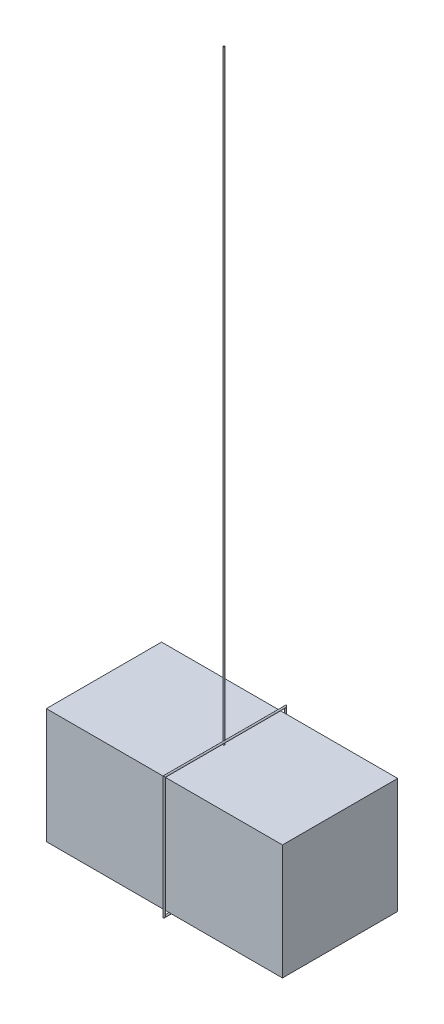
SolidWorks part; units mm, degrees
ref_plane "Front Plane" through (0, 0, 0) normal (0, 0, 1) x (1, 0, 0)
ref_plane "Top Plane" through (0, 0, 0) normal (0, 1, 0) x (1, 0, 0)
ref_plane "Right Plane" through (0, 0, 0) normal (1, 0, 0) x (0, 0, -1)
sketch "Sketch1" plane through (0, 0, 0) normal (0, 0, 1) x (1, 0, 0)
  line L0 (0, 0) -> (198.4375, 0)
  line L1 (198.4375, 0) -> (198.4375, -96.8375)
  line L2 (198.4375, -96.8375) -> (0, -96.8375)
  line L3 (0, -96.8375) -> (0, 0)
  dimension "D1" = 198.4375
  dimension "D2" = 96.8375
extrude "Extrude1" add sketch "Sketch1" along normal mid plane 96.8375
ref_plane "Plano1" through (101.6, 0, 0) normal (1, 0, 0) x (0, 0, -1)
sketch "Esboço1" plane through (101.6, 0, 0) normal (1, 0, 0) x (0, 0, -1)
  line L0 (48.4187, -96.8375) -> (48.4187, 0) construction
  line L1 (-50.9587, 2.54) -> (50.9587, 2.54)
  line L2 (-50.9587, 2.54) -> (-50.9588, -99.3775)
  line L3 (-50.9588, -99.3775) -> (50.9587, -99.3775)
  line L4 (50.9587, 2.54) -> (50.9587, -99.3775)
  line L5 (-50.9587, 2.54) -> (50.9587, -99.3775) construction
  line L6 (-50.9588, -99.3775) -> (50.9587, 2.54) construction
  line L7 (-48.4187, 0) -> (48.4187, 0) construction
  line L9 (-48.4187, -96.8375) -> (48.4187, -96.8375) construction
  point P0 (0, -48.4187)
  dimension "D1" = 2.54
  dimension "D2" = 2.54
  dimension "D3" = 2.54
sketch "Esboço2" plane through (0, 0, 0) normal (0, 0, 1) x (1, 0, 0)
  line L0 (101.6, 2.54) -> (101.6, -99.3775) construction
  line L1 (101.6, 2.54) -> (101.6, -99.3775) construction
  circle A0 centre (101.6, 2.54) radius 0.7144
sweep "Varredura1" add profiles "Esboço2" path "Esboço1"
sketch "Esboço3" plane through (0, 0, 0) normal (0, 1, 0) x (1, 0, 0)
  line L0 (100.8856, 50.9588) -> (100.8856, -50.9587) construction
  circle A0 centre (100.8856, 0) radius 0.635
  dimension "D1" = 1.27
extrude "Ressalto-extrusão1" add sketch "Esboço3" along normal blind 508
